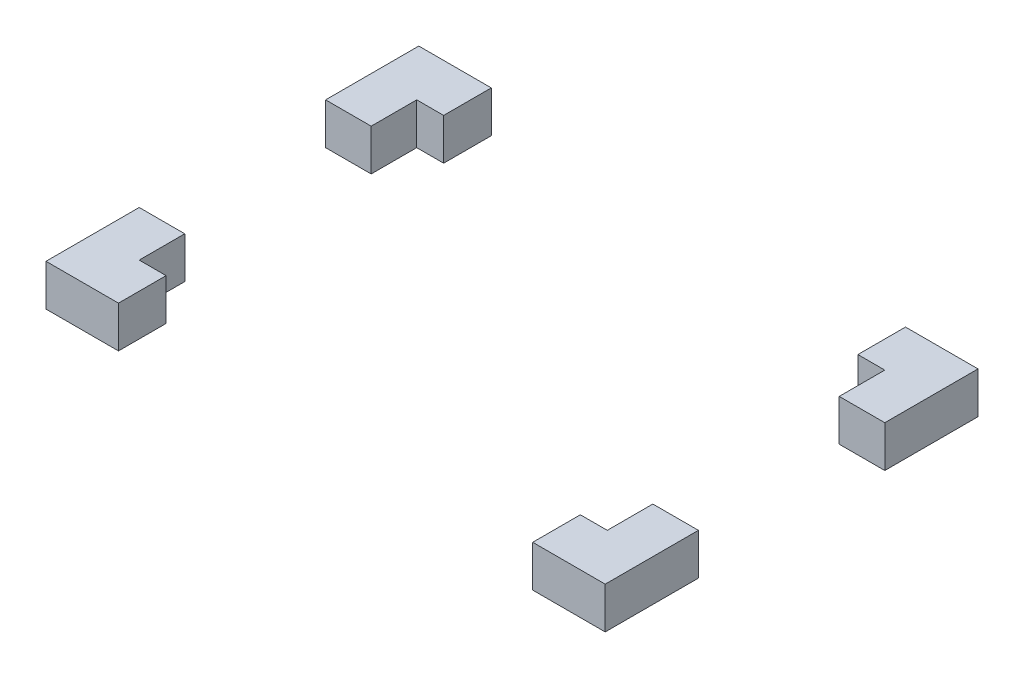
SolidWorks part; units mm, degrees
ref_plane "Front Plane" through (0, 0, 0) normal (0, 0, 1) x (1, 0, 0)
ref_plane "Top Plane" through (0, 0, 0) normal (0, 1, 0) x (1, 0, 0)
ref_plane "Right Plane" through (0, 0, 0) normal (1, 0, 0) x (0, 0, -1)
sketch "Sketch1" plane through (0, 0, 0) normal (0, 1, 0) x (1, 0, 0)
  line L1 (-67.5, 45) -> (67.5, 45)
  line L2 (-67.5, 45) -> (-67.5, -45)
  line L3 (-67.5, -45) -> (67.5, -45)
  line L4 (67.5, 45) -> (67.5, -45)
  line L5 (-56.5, 33.5) -> (56.5, 33.5)
  line L6 (-56.5, 33.5) -> (-56.5, -33.5)
  line L7 (-56.5, -33.5) -> (56.5, -33.5)
  line L8 (56.5, 33.5) -> (56.5, -33.5)
extrude "Boss-Extrude1" add sketch "Sketch1" along normal blind 10
sketch "Sketch2" plane through (56.5, 0, 0) normal (-1, 0, 0) x (0, 0, 1)
  line L1 (-22.5, 15) -> (22.5, 15)
  line L2 (-22.5, 15) -> (-22.5, -20)
  line L3 (-22.5, -20) -> (22.5, -20)
  line L4 (22.5, 15) -> (22.5, -20)
extrude "Cut-Extrude1" cut sketch "Sketch2" against normal mid plane 600
sketch "Sketch3" plane through (0, 10, 0) normal (0, 1, 0) x (1, 0, 0)
  line L1 (-50, 58.8496) -> (50, 58.8496)
  line L2 (-50, 58.8496) -> (-50, -61.7558)
  line L3 (-50, -61.7558) -> (50, -61.7558)
  line L4 (50, 58.8496) -> (50, -61.7558)
extrude "Cut-Extrude2" cut sketch "Sketch3" against normal mid plane 50
